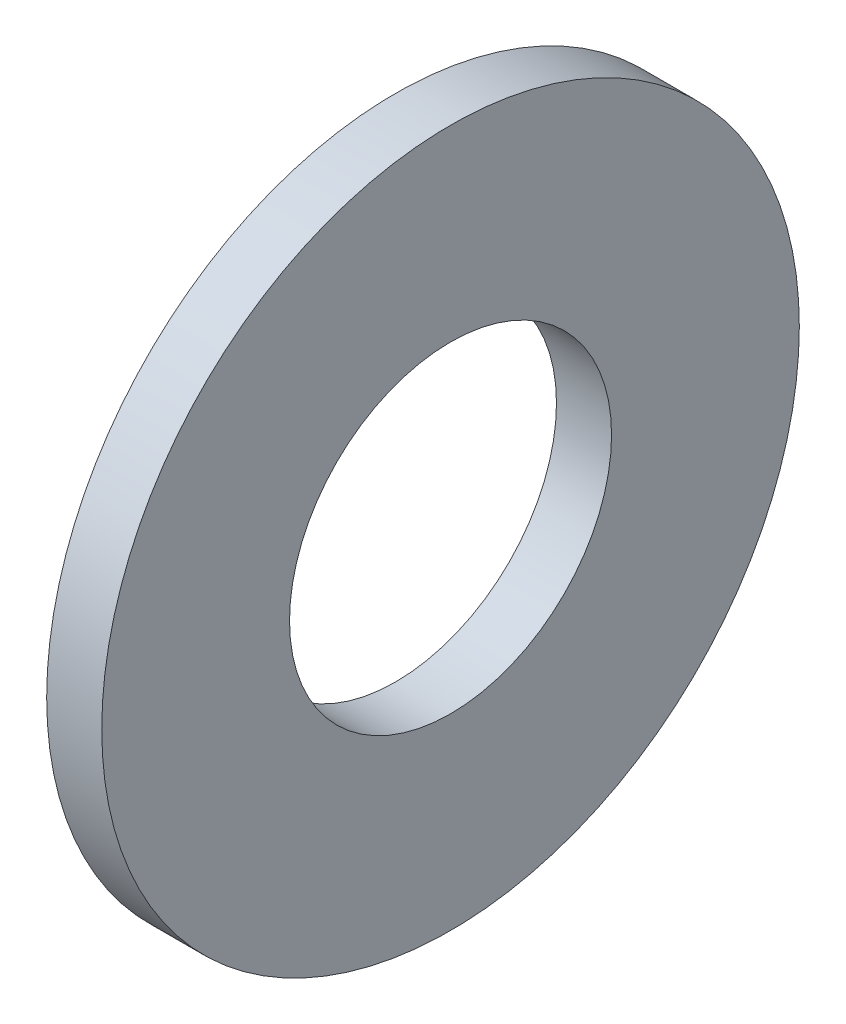
SolidWorks part; units mm, degrees
material "Alumina"
ref_plane "Front Plane" through (0, 0, 0) normal (0, 0, 1) x (1, 0, 0)
ref_plane "Top Plane" through (0, 0, 0) normal (0, 1, 0) x (1, 0, 0)
ref_plane "Right Plane" through (0, 0, 0) normal (1, 0, 0) x (0, 0, -1)
sketch "Sketch1" plane through (0, 0, 0) normal (0, 0, 1) x (1, 0, 0)
  line L0 (-16.7627, -2.0938) -> (34.5053, -2.0938) construction
  line L1 (-16.7627, -2.5938) -> (-16.7627, -1.5938) construction
  line L2 (34.5053, -5.0938) -> (34.5053, 0.9062) construction
  line L3 (16.4089, -10.865) -> (16.4089, 6.6773) construction
  line L4 (16.4089, 6.6773) -> (19.4089, 6.6773)
  line L5 (16.4089, 6.6773) -> (16.4089, 16.9062)
  line L6 (16.4089, 16.9062) -> (19.4089, 16.9062)
  line L7 (19.4089, 6.6773) -> (19.4089, 16.9062)
  line L8 (16.4089, -19.7112) -> (16.4089, 15.5236) construction
  dimension "D1" = 19
  dimension "D2" = 3
revolve "Revolve1" add sketch "Sketch1" angle 360 about L0
